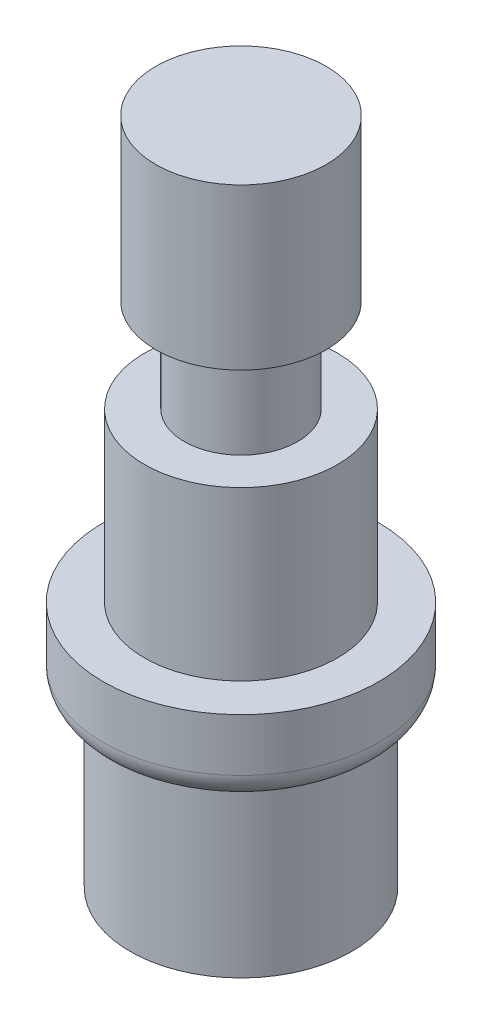
SolidWorks part; units mm, degrees
ref_plane "Front Plane" through (0, 0, 0) normal (0, 0, 1) x (1, 0, 0)
ref_plane "Top Plane" through (0, 0, 0) normal (0, 1, 0) x (1, 0, 0)
ref_plane "Right Plane" through (0, 0, 0) normal (1, 0, 0) x (0, 0, -1)
sketch "Sketch1" plane through (0, 0, 0) normal (0, 0, 1) x (1, 0, 0)
  line L0 (0, 0) -> (0, 23.55) construction
  line L1 (0, 23.55) -> (3, 23.55)
  line L2 (3, 23.55) -> (3, 17.9)
  line L3 (3, 17.9) -> (2, 17.9)
  line L4 (2, 17.9) -> (2, 14.6)
  line L5 (2, 14.6) -> (3.4, 14.6)
  line L6 (3.4, 14.6) -> (3.4, 8.7)
  line L7 (3.4, 8.7) -> (4.85, 8.7)
  line L8 (4.85, 8.7) -> (4.85, 6.845)
  line L9 (3.905, 5.9) -> (3.905, 0)
  line L10 (3.905, 0) -> (0, 0)
  line L11 (0, 0) -> (0, 23.55)
  arc A0 (4.85, 6.845) -> (3.905, 5.9) centre (3.905, 6.845) cw
  point P13 (1.3019, -2.9117)
  point P14 (5.1724, 7.1674)
  point P16 (0, 0)
  point P17 (0.1627, -0.1262)
  dimension "D1" = 5.65
  dimension "D2" = 3.3
  dimension "D3" = 5.9
  dimension "D4" = 2.8
  dimension "D5" = 5.9
  dimension "D6" = 6
  dimension "D7" = 4
  dimension "D8" = 6.8
  dimension "D9" = 9.7
  dimension "D10" = 7.81
revolve "Revolve1" add sketch "Sketch1" angle 360 about L0
